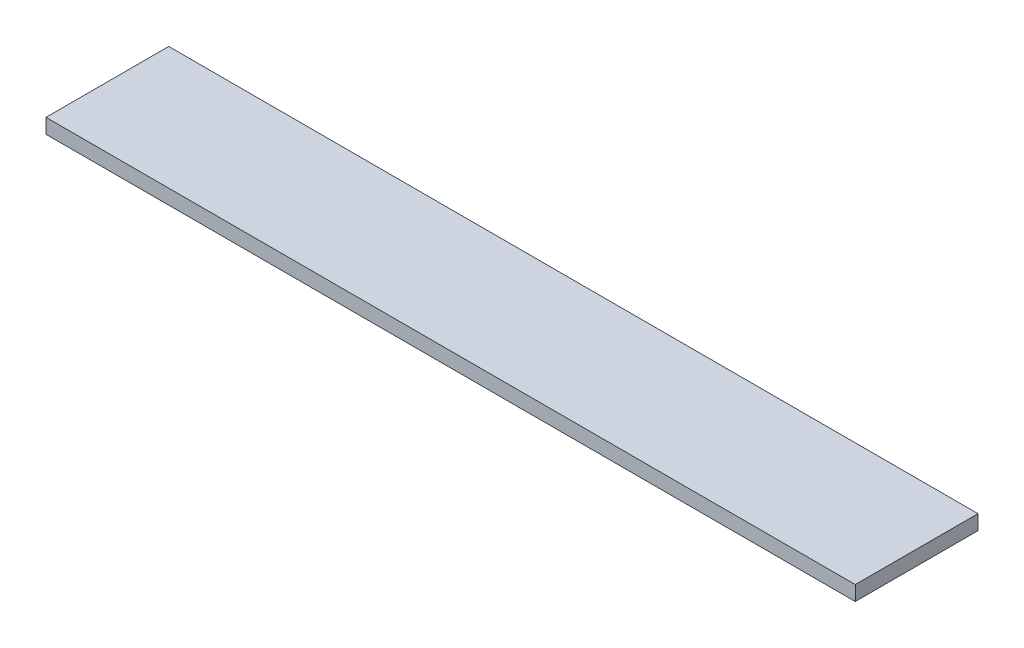
SolidWorks part; units mm, degrees
ref_plane "Front Plane" through (0, 0, 0) normal (0, 0, 1) x (1, 0, 0)
ref_plane "Top Plane" through (0, 0, 0) normal (0, 1, 0) x (1, 0, 0)
ref_plane "Right Plane" through (0, 0, 0) normal (1, 0, 0) x (0, 0, -1)
sketch "Sketch1" plane through (0, 0, 0) normal (0, 1, 0) x (1, 0, 0)
  line L1 (494.5, -75) -> (-494.5, -75)
  line L2 (494.5, -75) -> (494.5, 75)
  line L3 (494.5, 75) -> (-494.5, 75)
  line L4 (-494.5, -75) -> (-494.5, 75)
  line L5 (494.5, -75) -> (-494.5, 75) construction
  line L6 (494.5, 75) -> (-494.5, -75) construction
  point P0 (0, 0)
  dimension "D1" = 150
  dimension "D2" = 989
extrude "Boss-Extrude1" add sketch "Sketch1" along normal blind 18
equation "\"H_DSP\"=18"
equation "\"D1@Boss-Extrude1\"=\"H_DSP\""
